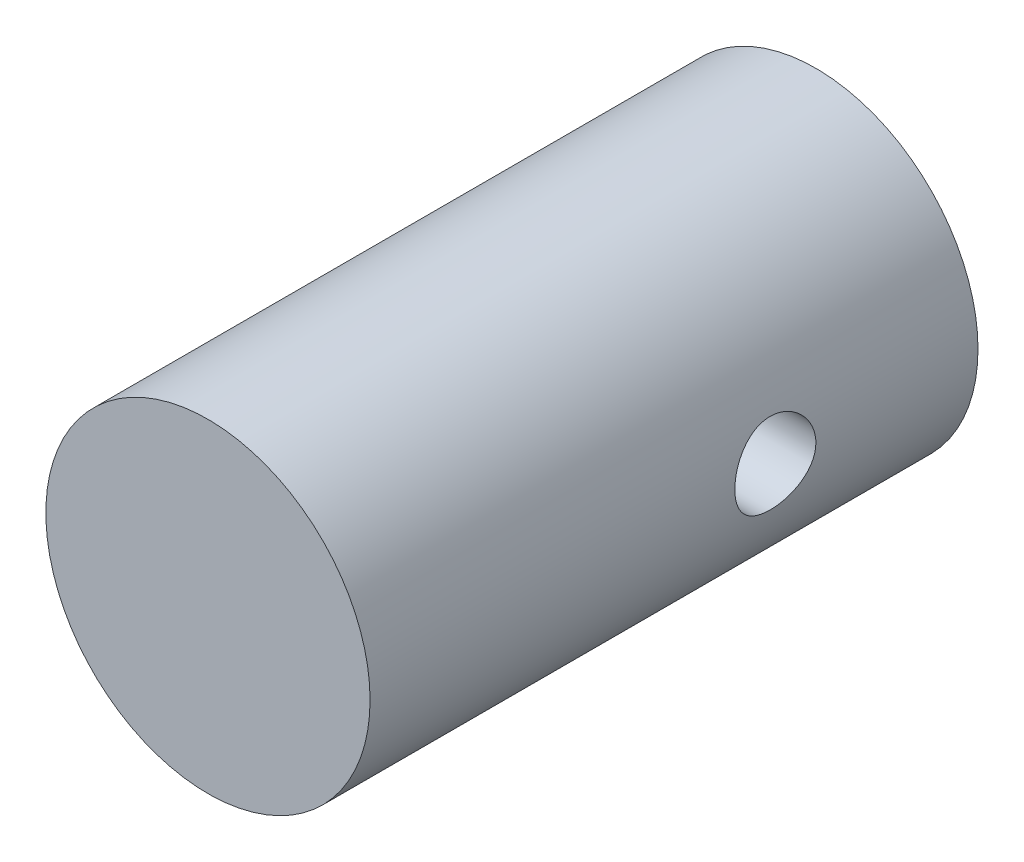
SolidWorks part; units mm, degrees
ref_plane "前视基准面" through (0, 0, 0) normal (0, 0, 1) x (1, 0, 0)
ref_plane "上视基准面" through (0, 0, 0) normal (0, 1, 0) x (1, 0, 0)
ref_plane "右视基准面" through (0, 0, 0) normal (1, 0, 0) x (0, 0, -1)
sketch "草图1" plane through (0, 0, 0) normal (0, 0, 1) x (1, 0, 0)
  circle A0 centre (-16.07, 15.5717) radius 8
  dimension "D1" = 16
extrude "凸台-拉伸1" add sketch "草图1" along normal blind 30
sketch "草图2" plane through (0, 0, 0) normal (1, 0, 0) x (0, 0, -1)
  line L0 (-30, 15.5717) -> (0, 15.5717) construction
  line L1 (-30, 23.5717) -> (-30, 7.5717) construction
  line L2 (0, 7.5717) -> (0, 23.5717) construction
  line L3 (0, 15.5717) -> (-10, 15.5717) construction
  circle A0 centre (-10, 15.5717) radius 2
  dimension "D1" = 10
  dimension "D2" = 4
extrude "切除-拉伸1" cut sketch "草图2" against normal blind 31
